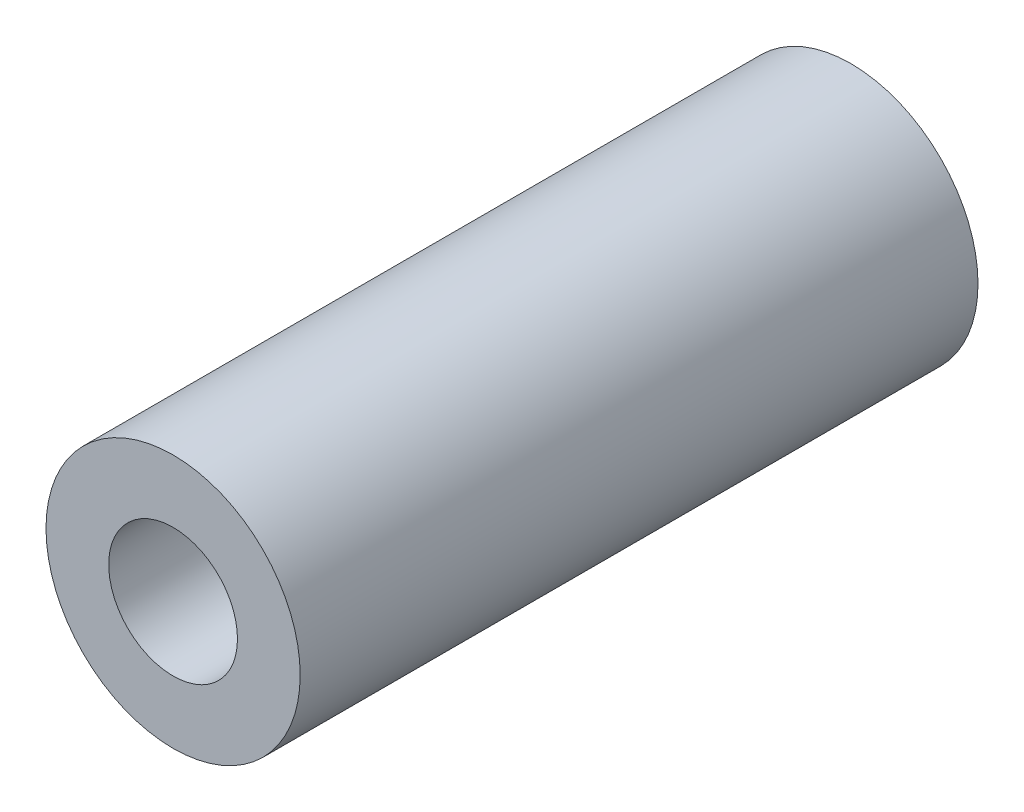
SolidWorks part; units mm, degrees
ref_plane "Front Plane" through (0, 0, 0) normal (0, 0, 1) x (1, 0, 0)
ref_plane "Top Plane" through (0, 0, 0) normal (0, 1, 0) x (1, 0, 0)
ref_plane "Right Plane" through (0, 0, 0) normal (1, 0, 0) x (0, 0, -1)
sketch "Sketch1" plane through (0, 0, 0) normal (0, 0, 1) x (1, 0, 0)
  circle A0 centre (0, 0) radius 9.525
  circle A1 centre (0, 0) radius 4.826
  dimension "OD" = 19.05
  dimension "ID" = 9.652
extrude "Extrude1" add sketch "Sketch1" along normal mid plane 50.8
sketch "Sketch2" plane through (0, 0, 0) normal (1, 0, 0) x (0, 0, -1)
  line L0 (-25.4, -4.826) -> (25.4, -4.826) construction
  line L3 (25.4, 4.826) -> (-25.4, 4.826) construction
  line L5 (-25.4, -4.826) -> (25.4, -4.826)
  line L6 (25.4, 4.826) -> (-25.4, 4.826)
sketch "Sketch4" plane through (0, 0, 25.4) normal (0, 0, 1) x (1, 0, 0)
  line L0 (0, 0) -> (-3.4125, 3.4125)
  line L1 (0, -2.1828) -> (0, 2.1828) construction
  circle A0 centre (0, 0) radius 4.826 construction
  dimension "D1" = 45
